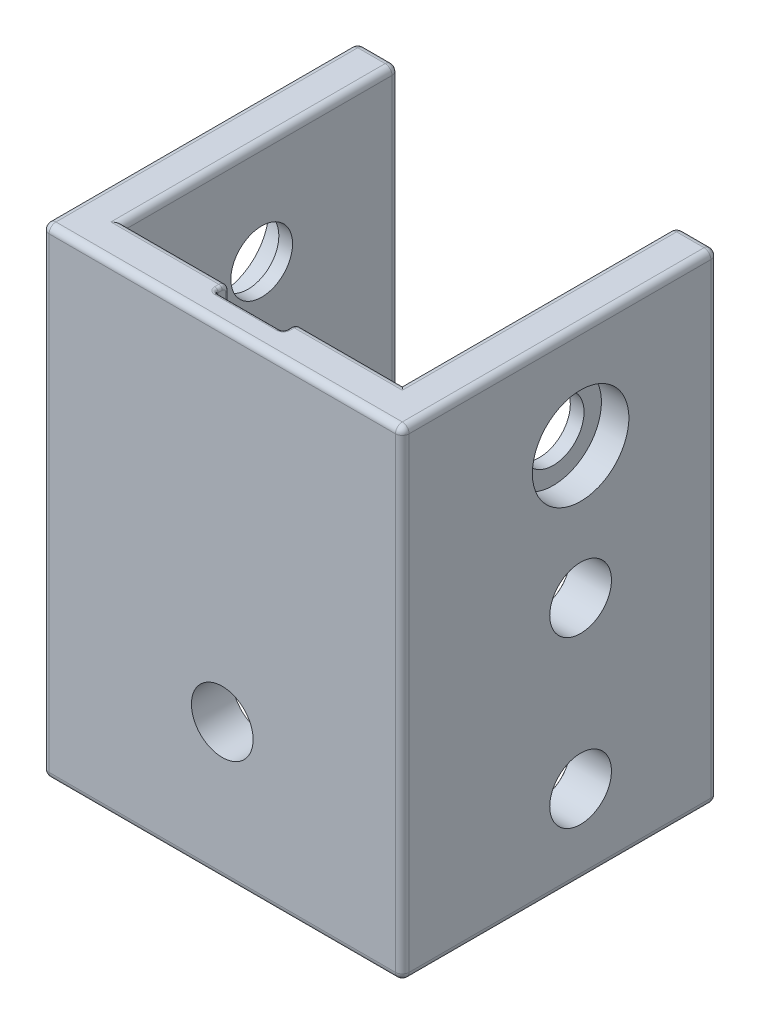
SolidWorks part; units mm, degrees
ref_plane "Front Plane" through (0, 0, 0) normal (0, 0, 1) x (1, 0, 0)
ref_plane "Top Plane" through (0, 0, 0) normal (0, 1, 0) x (1, 0, 0)
ref_plane "Right Plane" through (0, 0, 0) normal (1, 0, 0) x (0, 0, -1)
sketch "Sketch1" plane through (0, 0, 0) normal (0, 1, 0) x (1, 0, 0)
  line L1 (-26.25, -26.25) -> (26.25, -26.25)
  line L2 (-26.25, -26.25) -> (-26.25, 19.75)
  line L4 (26.25, -26.25) -> (26.25, 19.75)
  line L5 (-26.25, -26.25) -> (-20.25, -20.25) construction
  line L6 (20.25, -20.25) -> (26.25, -26.25) construction
  line L11 (-20.25, 19.75) -> (-20.25, -20.25)
  line L12 (-20.25, -20.25) -> (20.25, -20.25)
  line L20 (-20.25, 19.75) -> (-26.25, 19.75)
  line L21 (20.25, 19.75) -> (26.25, 19.75)
  line L22 (20.25, -20.25) -> (20.25, 19.75)
  point P0 (0, 0)
  point P5 (0, 0)
  point P47 (0, 0.8)
  point P49 (0, 0)
  dimension "D1" = 40.5
  dimension "D2" = 6
  dimension "D3" = 6
  dimension "D4" = 46
  dimension "D5" = 6
  dimension "D6" = 46
extrude "Boss-Extrude1" add sketch "Sketch1" along normal blind 70
ref_plane "Plane2" through (20.25, 0, -19.75) normal (1, 0, 0) x (0, 0, -1)
sketch "Sketch8" plane through (26.25, 0, 0) normal (1, 0, 0) x (0, 0, -1)
  line L0 (19.75, 70) -> (19.75, 0) construction
  line L2 (-26.25, 70) -> (19.75, 70) construction
  circle A0 centre (-0.25, 55) radius 4.5
  dimension "D1" = 20
  dimension "D3" = 9
  dimension "D2" = 15
extrude "Cut-Extrude4" cut sketch "Sketch8" against normal through all
sketch "Sketch10" plane through (-26.25, 0, 0) normal (-1, 0, 0) x (0, 0, 1)
  circle A0 centre (0.25, 55) radius 7.035
  dimension "D1" = 14.07
extrude "Cut-Extrude5" cut sketch "Sketch10" against normal blind 4
mirror "Mirror1" about plane through (0, 0, 0) normal (1, 0, 0) of "Cut-Extrude5"
fillet "Fillet13" radius 1 22 edges at (26.25, 0, 3.25) (0, 0, 26.25) (-26.25, 0, 3.25) (-23.25, 0, -19.75) (-26.25, 35, 26.25) (0, 70, 26.25) (-26.25, 70, 3.25) (23.25, 70, -19.75) (-23.25, 70, -19.75) (26.25, 70, 3.25) (26.25, 35, -19.75) (-26.25, 35, -19.75) (26.25, 35, 26.25) (23.25, 0, -19.75) (20.25, 0, 0.25) (-20.25, 0, 0.25) (0, 0, 20.25) (20.25, 70, 0.25) (-20.25, 70, 0.25) (0, 70, 20.25) (-20.25, 35, -19.75) (20.25, 35, -19.75)
sketch "Sketch15" plane through (-26.25, 0, 0) normal (-1, 0, 0) x (0, 0, 1)
  line L0 (-19.75, 1) -> (-19.75, 69) construction
  line L1 (-18.75, 70) -> (25.25, 70) construction
  point P0 (-14.75, 40)
  point P2 (15.25, 40)
  point P4 (15.25, 15)
  point P6 (-14.75, 15)
  dimension "D1" = 5
  dimension "D2" = 35
  dimension "D3" = 25
  dimension "D4" = 30
hole_wizard "M8 Clearance Hole1" positions "Sketch19" profile "Sketch18" hole size "M8" standard "ANSI Metric"
sketch "Sketch19" plane through (-20.25, 0, 0) normal (1, 0, 0) x (0, 0, -1)
  line L0 (19.75, 69) -> (19.75, 1) construction
  point P0 (-0.25, 35.7862)
  point P2 (-0.25, 11.6767)
  point P7 (0, 0)
  dimension "D1" = 20
  dimension "D2" = 20
sketch "Sketch18" plane through (-20.25, 35.7862, 0.25) normal (0, 1, 0) x (0, 0, -1)
  line L0 (0, 0) -> (0, 15.7039)
  line L1 (0, 15.7039) -> (4.5, 13)
  line L2 (4.5, 13) -> (4.5, 0.025)
  line L3 (4.5, 0.025) -> (4.525, 0)
  line L5 (4.525, 0) -> (0, 0)
  line L6 (-4.5, 0.025) -> (-4.525, 0) construction
  line L10 (0, 15.7039) -> (-4.5, 13) construction
  line L11 (0, -6.35) -> (0, 107.95) construction
  dimension "Hole Dia." = 9
  dimension "Hole Depth" = 13
  dimension "Near C'Sink Dia." = 9.05
  dimension "Near C'Sink Angle" = 90
  dimension "Drill Angle" = 118
mirror "Mirror2" about plane through (0, 0, 0) normal (1, 0, 0) of "M8 Clearance Hole1"
ref_plane "Plane3" through (0, 0, 0) normal (1, 0, 0) x (0, 0, -1)
sketch "Sketch20" plane through (0, 0, 0) normal (1, 0, 0) x (0, 0, -1)
  circle A0 centre (-0.25, 55) radius 4.5 construction
  circle A1 centre (-0.25, 55) radius 4.5
sketch "Sketch21" plane through (-26.25, 0, 0) normal (-1, 0, 0) x (0, 0, 1)
  line L0 (-19.75, 1) -> (-19.75, -1.1939) construction
  line L1 (-19.75, 0) -> (10.25, 0)
  line L2 (-19.75, 0) -> (-19.75, 26.5)
  line L3 (-19.75, 26.5) -> (10.25, 26.5)
  line L4 (10.25, 0) -> (10.25, 26.5)
  line L5 (-18.5203, 0) -> (-20.9952, 0) construction
  line L6 (25.25, 0) -> (-18.75, 0) construction
  dimension "D1" = 26.5
  dimension "D2" = 30
extrude "Cut-Extrude6" cut sketch "Sketch21" against normal up to next
sketch "Sketch22" plane through (0, 0, 26.25) normal (0, 0, 1) x (1, 0, 0)
  line L0 (0, 0) -> (0, 34.976) construction
  line L1 (0, -21.45) -> (0, 21.45) construction
  line L2 (25.25, 0) -> (-25.25, 0) construction
  point P5 (0, 20)
  dimension "D1" = 20
hole_wizard "M8 Clearance Hole2" positions "Sketch22" profile "Sketch23" hole size "M8" standard "ANSI Metric" end condition through all
sketch "Sketch23" plane through (0, 20, 26.25) normal (1, 0, 0) x (0, -1, 0)
  line L0 (0, 0) -> (0, 46)
  line L1 (0, 46) -> (4.5, 46)
  line L2 (4.5, 46) -> (4.5, 0)
  line L5 (4.5, 0) -> (0, 0)
  line L11 (0, -6.35) -> (0, 107.95) construction
  dimension "Thru Hole Dia." = 9
  dimension "Thru Hole Depth" = 46
fillet "Fillet14" radius 5 1 edges at (-23.25, 26.5, 10.25)
sketch "Sketch24" plane through (0, 0, 20.25) normal (0, 0, -1) x (-1, 0, 0)
  line L0 (-21.25, 70) -> (21.25, 70) construction
  line L1 (-5, 32) -> (5, 32)
  line L2 (-5, 32) -> (-5, 70)
  line L3 (-5, 70) -> (5, 70)
  line L4 (5, 32) -> (5, 70)
  line L5 (-5, 32) -> (5, 70) construction
  line L6 (-5, 70) -> (5, 32) construction
  point P0 (0, 51)
  point P7 (0, 32)
  dimension "D1" = 38
  dimension "D2" = 10
extrude "Cut-Extrude7" cut sketch "Sketch24" against normal blind 2.1
fillet "Fillet15" radius 0.5 13 edges at (5, 69.7071, 20.5429) (-5, 69.7071, 20.5429) (5, 70, 21.8) (-5, 70, 21.8) (5, 50.5, 20.25) (-5, 50.5, 20.25) (0, 32, 22.35) (5, 51, 22.35) (0, 70, 22.35) (-5, 51, 22.35) (5, 32, 21.3) (-5, 32, 21.3) (0, 32, 20.25)
